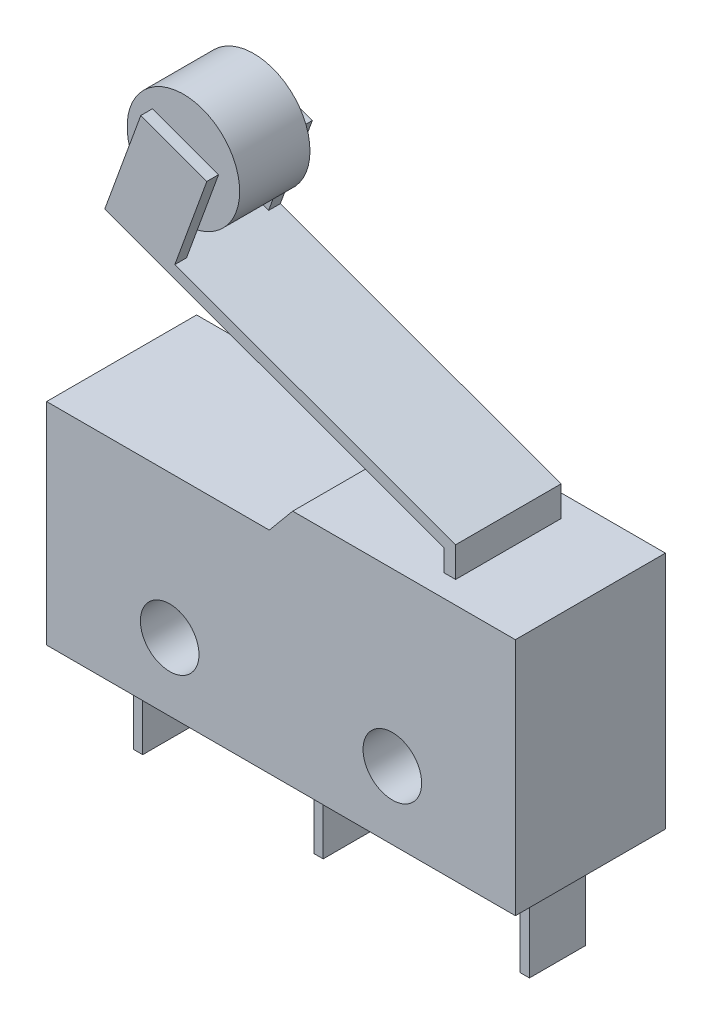
SolidWorks part; units mm, degrees
ref_plane "Alzado" through (0, 0, 0) normal (0, 0, 1) x (1, 0, 0)
ref_plane "Planta" through (0, 0, 0) normal (0, 1, 0) x (1, 0, 0)
ref_plane "Vista lateral" through (0, 0, 0) normal (1, 0, 0) x (0, 0, -1)
sketch "Croquis1" plane through (0, 0, 0) normal (0, 0, 1) x (1, 0, 0)
  line L0 (0, 9) -> (9.5, 9)
  line L1 (0, 0) -> (20, 0)
  line L2 (0, 0) -> (0, 9)
  line L3 (10.5, 10.2) -> (20, 10.2)
  line L4 (20, 0) -> (20, 10.2)
  line L5 (9.5, 9) -> (10.5, 10.2)
  circle A0 centre (5.25, 2.9) radius 1.25
  circle A1 centre (14.75, 2.9) radius 1.25
  dimension "D9" = 2.5
  dimension "D1" = 20
  dimension "D2" = 10.2
  dimension "D3" = 9
  dimension "D4" = 9.5
  dimension "D5" = 9.5
  dimension "D6" = 2.9
  dimension "D7" = 5.25
  dimension "D8" = 5.25
extrude "Saliente-Extruir1" add sketch "Croquis1" along normal mid plane 6.4
sketch "Croquis2" plane through (0, 0, 0) normal (0, -1, 0) x (1, 0, 0)
  line L0 (20, 3.2) -> (20, -3.2) construction
  line L1 (1.7, 1.2) -> (2.1, 1.2)
  line L2 (1.7, 1.2) -> (1.7, -1.2)
  line L3 (1.7, -1.2) -> (2.1, -1.2)
  line L4 (2.1, 1.2) -> (2.1, -1.2)
  line L5 (9.4, 1.2) -> (9.8, 1.2)
  line L6 (9.4, 1.2) -> (9.4, -1.2)
  line L7 (9.4, -1.2) -> (9.8, -1.2)
  line L8 (9.8, 1.2) -> (9.8, -1.2)
  line L9 (18.2, 1.2) -> (18.6, 1.2)
  line L10 (18.2, 1.2) -> (18.2, -1.2)
  line L11 (18.2, -1.2) -> (18.6, -1.2)
  line L12 (18.6, 1.2) -> (18.6, -1.2)
  line L13 (0, 3.2) -> (20, 3.2) construction
  line L14 (0, -3.2) -> (20, -3.2) construction
  dimension "D1" = 1.4
  dimension "D2" = 0.4
  dimension "D3" = 2
  dimension "D4" = 2
  dimension "D5" = 8.4
  dimension "D6" = 7.3
extrude "Saliente-Extruir2" add sketch "Croquis2" along normal blind 4
sketch "Croquis3" plane through (0, 0, 0) normal (0, 0, 1) x (1, 0, 0)
  line L0 (16, 10.2) -> (16, 11.1331)
  line L1 (20, 10.2) -> (10.5, 10.2) construction
  line L2 (20, 0) -> (20, 10.2) construction
  line L5 (16.5, 11.4832) -> (16.5, 10.2)
  line L6 (16.5, 10.2) -> (16, 10.2)
  line L7 (1.5294, 16.4) -> (16, 11.1331)
  line L8 (16.5, 11.4832) -> (1.7004, 16.8698)
  line L9 (1.7004, 16.8698) -> (1.5294, 16.4)
  circle A1 centre (5.25, 2.9) radius 1.25 construction
  dimension "D1" = 0.5
  dimension "D2" = 0.5
  dimension "D3" = 3.5
  dimension "D4" = 15.7494
  dimension "D5" = 20
  dimension "D6" = 13.5
extrude "Saliente-Extruir3" add sketch "Croquis3" along normal mid plane 4.5
sketch "Croquis4" plane through (5.6208, 15.443, 0) normal (0.342, 0.9397, 0) x (0.9397, -0.342, 0)
  line L1 (-4.1719, 2.25) -> (-1.1719, 2.25)
  line L2 (-4.1719, 2.25) -> (-4.1719, 1.75)
  line L3 (-4.1719, 1.75) -> (-1.1719, 1.75)
  line L4 (-1.1719, 2.25) -> (-1.1719, 1.75)
  line L5 (-4.1719, -2.25) -> (-1.1719, -2.25)
  line L6 (-4.1719, -2.25) -> (-4.1719, -1.75)
  line L7 (-4.1719, -1.75) -> (-1.1719, -1.75)
  line L8 (-1.1719, -2.25) -> (-1.1719, -1.75)
  dimension "D1" = 0.5
  dimension "D2" = 3
extrude "Saliente-Extruir4" add sketch "Croquis4" along normal blind 4
sketch "Croquis5" plane through (0, 0, 0) normal (0, 0, 1) x (1, 0, 0)
  line L0 (4.4781, 20.1156) -> (2.939, 15.887) construction
  line L1 (3.0685, 20.6286) -> (5.8876, 19.6026) construction
  line L2 (1.5294, 16.4) -> (16, 11.1331) construction
  circle A0 centre (4.136, 19.1759) radius 2.4
  dimension "D1" = 4.8
  dimension "D2" = 1
extrude "Saliente-Extruir5" add sketch "Croquis5" along normal mid plane 3
sketch "Croquis6" plane through (0, 0, 0) normal (0, 0, 1) x (1, 0, 0)
  line L7 (2.991, 12.8864) -> (2.9608, 11.7603) construction
  line L8 (-0.0079, 12.9667) -> (-0.0515, 11.3408) construction
  line L10 (-0.0515, 11.3408) -> (15.3423, 10.9285) construction
  line L11 (15.7056, 11.419) -> (2.9608, 11.7603) construction
  arc A0 (4.7087, 23.1094) -> (-1.954, 9.0077) centre (16.3005, 9.0077) ccw construction
  arc A1 (5.8117, 21.7676) -> (-0.2171, 9.0077) centre (16.3005, 9.0077) ccw construction
  arc A2 (5.6437, 21.9719) -> (-0.4816, 9.0077) centre (16.3005, 9.0077) ccw construction
  arc A3 (2.991, 12.8864) -> (-0.0079, 12.9667) centre (1.5417, 14.7994) ccw construction
  arc A4 (7.4972, 19.717) -> (2.4374, 9.0077) centre (16.3005, 9.0077) ccw construction
  arc A5 (7.6512, 19.5297) -> (2.6798, 9.0077) centre (16.3005, 9.0077) ccw construction
  circle A6 centre (16.3005, 9.0077) radius 2.1466 construction
  circle A7 centre (16.3005, 9.0077) radius 2.4835 construction
  dimension "D1" = 3.5
  dimension "D2" = 1.6265
  dimension "D3" = 1.1265
  dimension "D4" = 15.3993
  dimension "D5" = 12.7494
